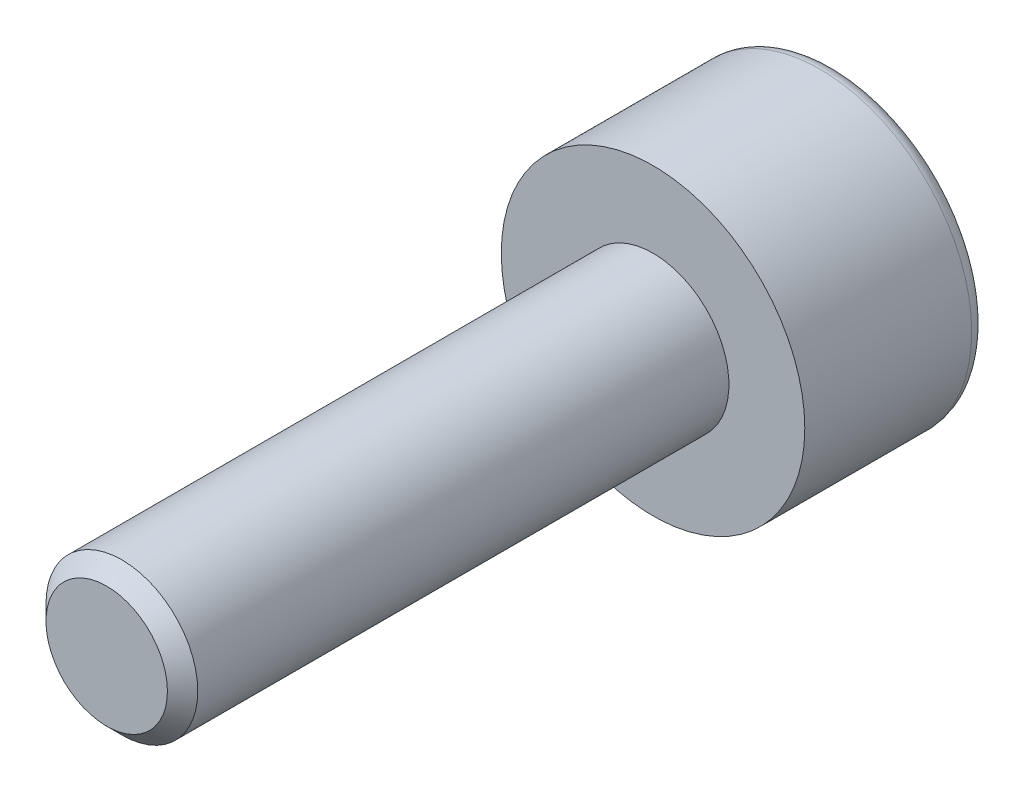
SolidWorks part; units mm, degrees
ref_plane "Plan1" through (0, 0, 0) normal (0, 0, 1) x (1, 0, 0)
ref_plane "Plan2" through (0, 0, 0) normal (0, 1, 0) x (1, 0, 0)
ref_plane "Plan3" through (0, 0, 0) normal (1, 0, 0) x (0, 0, -1)
sketch "Esquisse1" plane through (0, 0, 0) normal (0, 0, 1) x (1, 0, 0)
  circle A0 centre (0, 0) radius 2.5
  dimension "D1" = 5
extrude "Base-Extrusion" add sketch "Esquisse1" along normal blind 18
cosmetic thread "Représentation de filetage1" parameters "D1"=16, "D2"=0
chamfer "Chanfrein1" distance 0.5 angle 45
sketch "Esquisse2" plane through (0, 0, 0) normal (0, 0, -1) x (-1, 0, 0)
  circle A0 centre (0, 0) radius 5
  dimension "D1" = 10
extrude "Boss.-Extru.1" add sketch "Esquisse2" along normal blind 6
sketch "Esquisse3" plane through (0, 0, -6) normal (0, 0, -1) x (-1, 0, 0)
  line L0 (0, -3.87) -> (0, 4.26) construction
  line L1 (-3.91, 0) -> (3.72, 0) construction
  line L2 (-3, 0) -> (-1.5, 2.5981)
  line L3 (-1.5, 2.5981) -> (1.5, 2.5981)
  line L4 (3, 0) -> (1.5, 2.5981)
  line L5 (3, 0) -> (1.5, -2.5981)
  line L6 (-1.5, -2.5981) -> (1.5, -2.5981)
  line L7 (-3, 0) -> (-1.5, -2.5981)
  point P11 (0, 2.5981)
  dimension "D2" = 120
extrude "Enlèv. mat.-Extru.1" cut sketch "Esquisse3" against normal blind 3
sketch "Esquisse4" plane through (0, 0, -6) normal (0, 0, -1) x (-1, 0, 0)
  circle A0 centre (0, 0) radius 3
extrude "Enlèv. mat.-Extru.2" cut sketch "Esquisse4" against normal blind 0.5 draft 45
fillet "Congé1" radius 0.5
